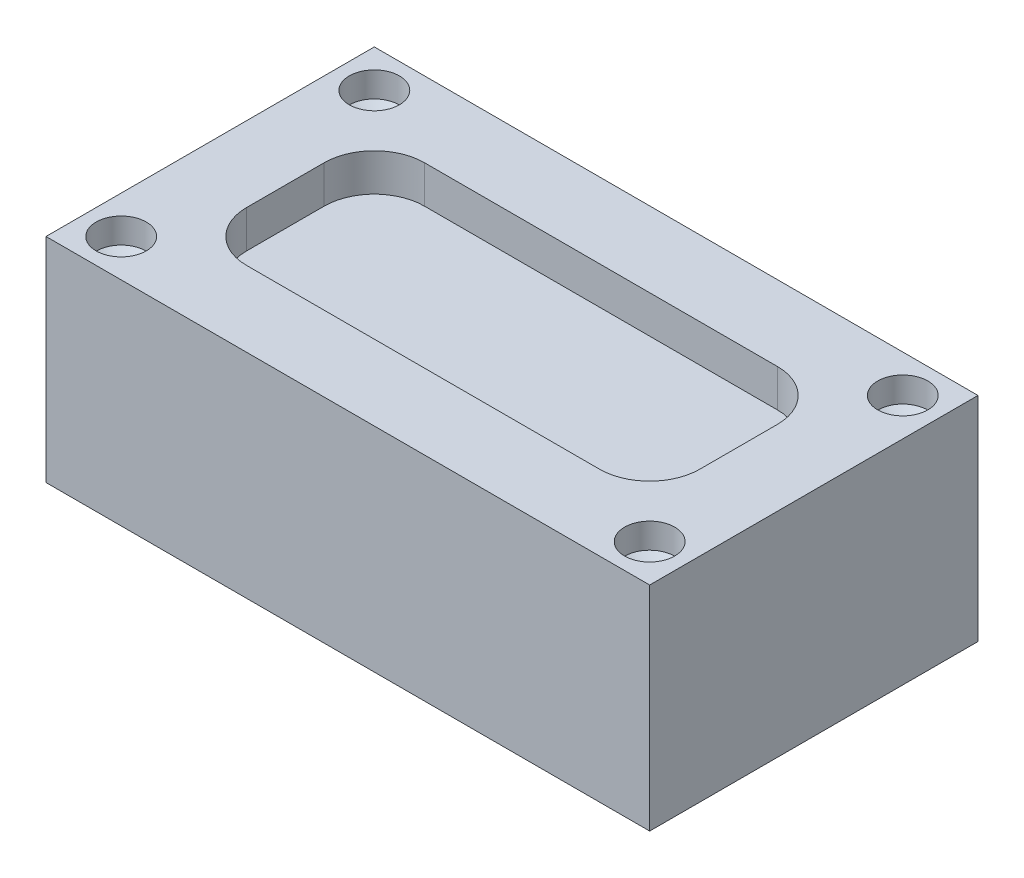
SolidWorks part; units mm, degrees
ref_plane "Front Plane" through (0, 0, 0) normal (0, 0, 1) x (1, 0, 0)
ref_plane "Top Plane" through (0, 0, 0) normal (0, 1, 0) x (1, 0, 0)
ref_plane "Right Plane" through (0, 0, 0) normal (1, 0, 0) x (0, 0, -1)
sketch "Sketch3" plane through (0, 0, 0) normal (0, 1, 0) x (1, 0, 0)
  line L1 (-120.3827, -65.4738) -> (120.3827, -65.4738)
  line L2 (-120.3827, -65.4738) -> (-120.3827, 65.4738)
  line L3 (-120.3827, 65.4738) -> (120.3827, 65.4738)
  line L4 (120.3827, -65.4738) -> (120.3827, 65.4738)
  line L5 (-120.3827, -65.4738) -> (120.3827, 65.4738) construction
  line L6 (-120.3827, 65.4738) -> (120.3827, -65.4738) construction
  point P0 (0, 0)
extrude "Boss-Extrude2" add sketch "Sketch3" along normal blind 85
sketch "Sketch4" plane through (0, 85, 0) normal (0, 1, 0) x (1, 0, 0)
  line L8 (90.3827, -35.4738) -> (90.3827, 35.4738)
  line L9 (90.3827, 35.4738) -> (-90.3827, 35.4738)
  line L10 (-90.3827, 35.4738) -> (-90.3827, -35.4738)
  line L11 (-90.3827, -35.4738) -> (90.3827, -35.4738)
  line L12 (90.3827, -35.4738) -> (90.3827, 35.4738)
  line L13 (90.3827, 35.4738) -> (-90.3827, 35.4738)
  line L14 (-90.3827, 35.4738) -> (-90.3827, -35.4738)
  line L15 (-90.3827, -35.4738) -> (90.3827, -35.4738)
  dimension "D1" = 30
extrude "Cut-Extrude1" cut sketch "Sketch4" against normal blind 15
sketch "Sketch5" plane through (0, 85, 0) normal (0, 1, 0) x (1, 0, 0)
  line L8 (105.3827, -50.4738) -> (105.3827, 50.4738)
  line L9 (105.3827, 50.4738) -> (-105.3827, 50.4738)
  line L10 (-105.3827, 50.4738) -> (-105.3827, -50.4738)
  line L11 (-105.3827, -50.4738) -> (105.3827, -50.4738)
  line L12 (105.3827, -50.4738) -> (105.3827, 50.4738) construction
  line L13 (105.3827, 50.4738) -> (-105.3827, 50.4738) construction
  line L14 (-105.3827, 50.4738) -> (-105.3827, -50.4738) construction
  line L15 (-105.3827, -50.4738) -> (105.3827, -50.4738) construction
  dimension "D1" = 15
hole_wizard "Ø20.0mm Dowel Hole1" positions "3DSketch2" profile "Sketch6" hole size "Ø20.0" standard "ANSI Metric"
sketch3d "3DSketch2"
  point P0 (-105.3827, 85, -50.4738)
  point P3 (-105.3827, 85, 50.4738)
  point P6 (105.3827, 85, -50.4738)
  point P9 (105.3827, 85, 50.4738)
sketch "Sketch6" plane through (-105.3827, 85, -50.4738) normal (1, 0, 0) x (0, 0, 1)
  line L0 (0, 0) -> (0, 16.0586)
  line L1 (0, 16.0586) -> (10, 10.05)
  line L2 (10, 10.05) -> (10, 0)
  line L5 (10, 0) -> (0, 0)
  line L10 (0, 16.0586) -> (-10, 10.05) construction
  line L11 (0, -6.35) -> (0, 107.95) construction
  dimension "Hole Dia." = 20
  dimension "Hole Depth" = 10.05
  dimension "Drill Angle" = 118
fillet "Fillet1" radius 20 4 edges at (-90.3827, 77.5, 35.4738) (90.3827, 77.5, 35.4738) (90.3827, 77.5, -35.4738) (-90.3827, 77.5, -35.4738)
